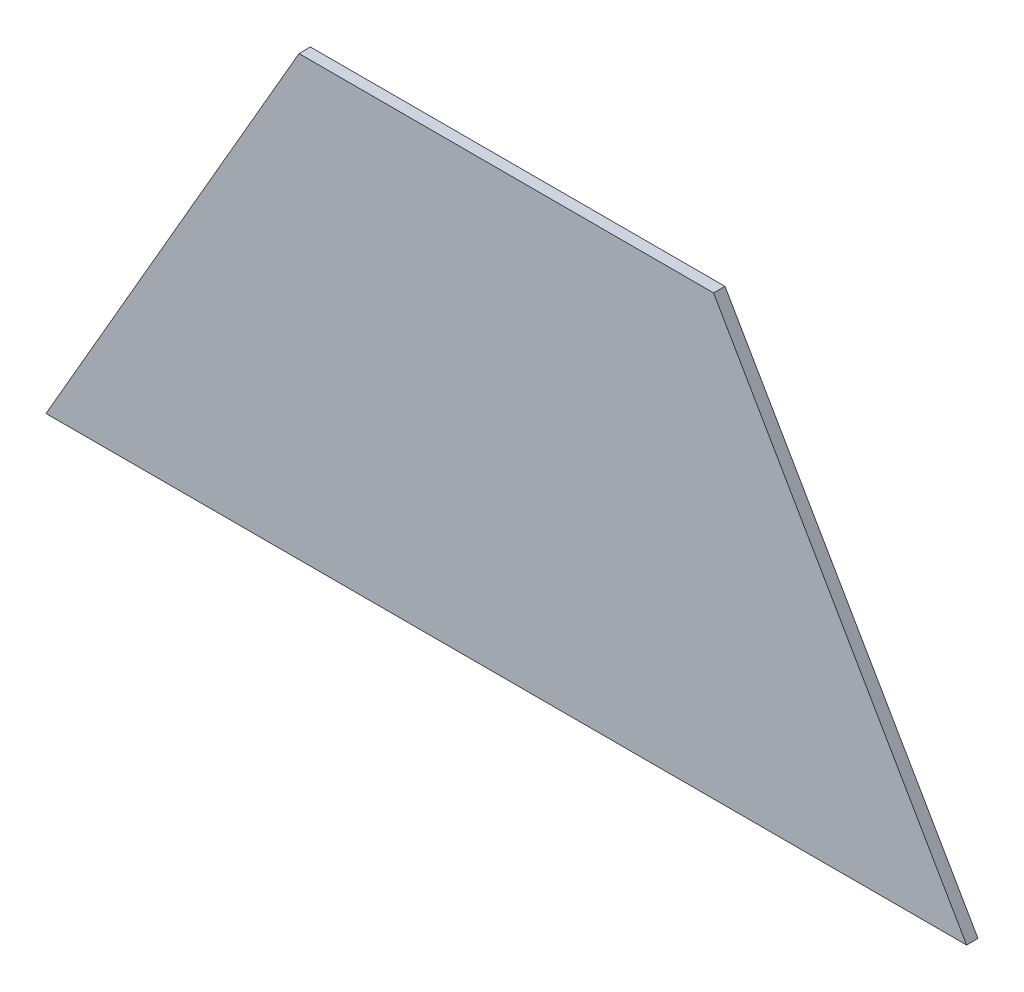
SolidWorks part; units mm, degrees
material "Pine"
ref_plane "Front Plane" through (0, 0, 0) normal (0, 0, 1) x (1, 0, 0)
ref_plane "Top Plane" through (0, 0, 0) normal (0, 1, 0) x (1, 0, 0)
ref_plane "Right Plane" through (0, 0, 0) normal (1, 0, 0) x (0, 0, -1)
sketch "Sketch1" plane through (0, 0, 0) normal (0, 0, 1) x (1, 0, 0)
  line L0 (-480.2035, -831.7368) -> (480.2035, -831.7368)
  line L1 (480.2035, -831.7368) -> (216.2389, -374.5368)
  line L2 (216.2389, -374.5368) -> (-216.2389, -374.5368)
  line L3 (-216.2389, -374.5368) -> (-480.2035, -831.7368)
  line L4 (480.2035, -831.7368) -> (-480.2035, -831.7368) construction
  line L5 (-480.2035, -831.7368) -> (-216.2389, -374.5368) construction
  line L6 (216.2389, -374.5368) -> (480.2035, -831.7368) construction
  line L7 (-216.2389, -374.5368) -> (216.2389, -374.5368) construction
extrude "Boss-Extrude1" add sketch "Sketch1" against normal up to surface (11.9063 mm away)
